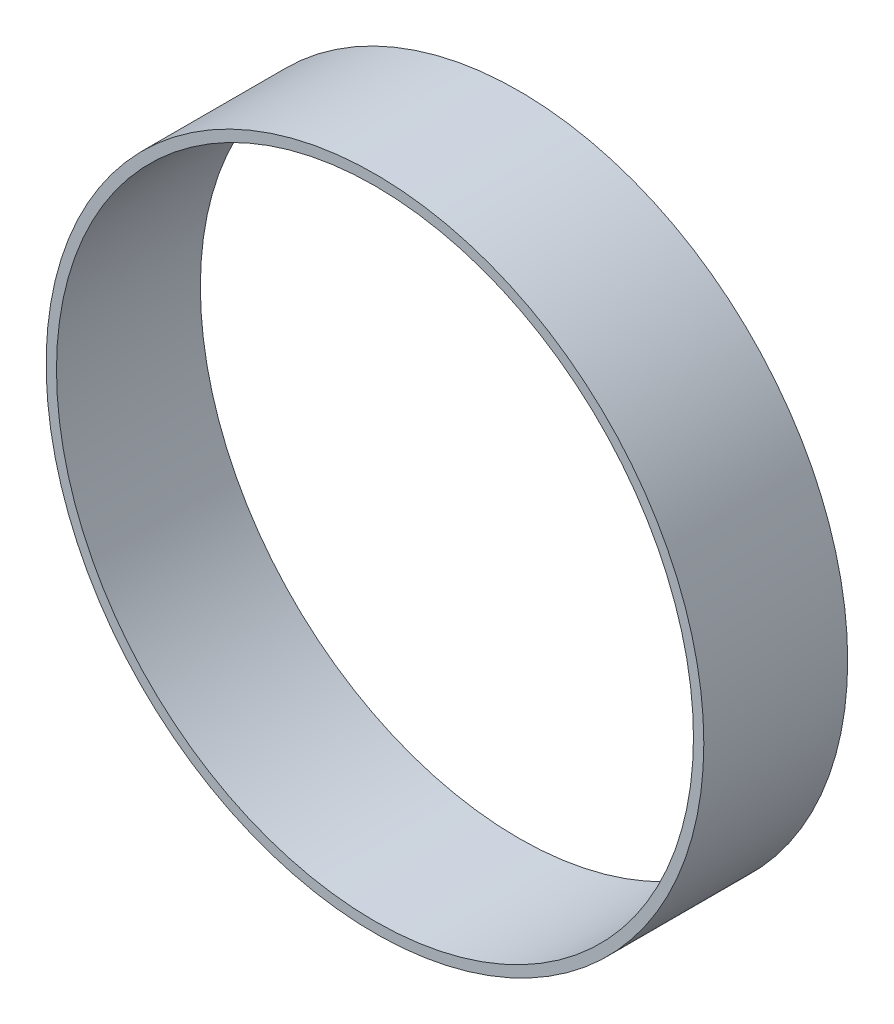
SolidWorks part; units mm, degrees
material "Plain Carbon Steel"
ref_plane "Front" through (0, 0, 0) normal (0, 0, 1) x (1, 0, 0)
ref_plane "Top" through (0, 0, 0) normal (0, 1, 0) x (1, 0, 0)
ref_plane "Right" through (0, 0, 0) normal (1, 0, 0) x (0, 0, -1)
ref_plane "Plane1" through (0, 0, 373.3022) normal (0, 0, 1) x (1, 0, 0)
sketch "Sketch2" plane through (0, 0, 373.3022) normal (0, 0, 1) x (1, 0, 0)
  circle A0 centre (0, 0) radius 101.6
  circle A1 centre (0, 0) radius 98.3996
  dimension "D1" = 203.2
  dimension "D2" = 3.2004
extrude "Extrude1" add sketch "Sketch2" against normal blind 44.45
